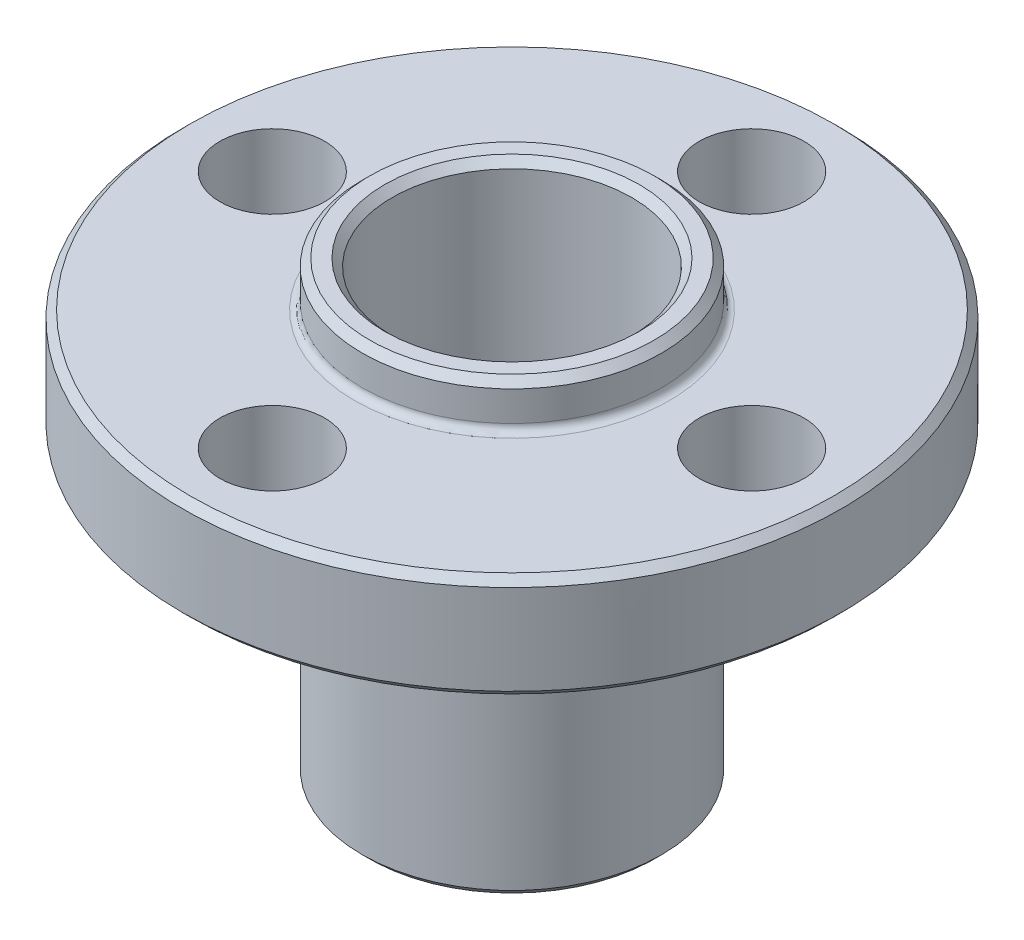
SolidWorks part; units mm, degrees
material "Ottone"
ref_plane "Piano frontale" through (0, 0, 0) normal (0, 0, 1) x (1, 0, 0)
ref_plane "Piano superiore" through (0, 0, 0) normal (0, 1, 0) x (1, 0, 0)
ref_plane "Piano destro" through (0, 0, 0) normal (1, 0, 0) x (0, 0, -1)
sketch "Schizzo1" plane through (0, 0, 0) normal (0, 0, 1) x (1, 0, 0)
  line L0 (0, 0) -> (0, 15)
  line L1 (0, 15) -> (1, 15)
  line L2 (1, 15) -> (1, 13.5)
  line L3 (1, 13.5) -> (7, 13.5)
  line L4 (7, 13.5) -> (7, 10)
  line L5 (7, 10) -> (1, 10)
  line L6 (1, 10) -> (1, 0)
  line L7 (0, 0) -> (1, 0)
  line L8 (0, 0) -> (-4, 0) construction
  line L9 (-4, 0) -> (-4, 18.9483) construction
  dimension "D1" = 3.5
  dimension "D2" = 10
  dimension "D3" = 1.5
  dimension "D4" = 1
  dimension "D5" = 7
  dimension "D7" = 4
revolve "Rivoluzione1" add sketch "Schizzo1" angle 360 about L9
sketch "Schizzo2" plane through (0, 13.5, 0) normal (0, 1, 0) x (1, 0, 0)
  line L0 (-4, 0) -> (-4, -29.8161) construction
  circle A0 centre (-4, -8) radius 1.75
  circle A1 centre (-12, 0) radius 1.75
  circle A2 centre (-4, 8) radius 1.75
  circle A3 centre (4, 0) radius 1.75
  point P6 (-4, 0)
  point P13 (-4, 0)
  dimension "D2" = 3.5
  dimension "D1" = 8
  dimension "D3" = 4
extrude "Taglio-Estrusione1" cut sketch "Schizzo2" against normal blind 10
chamfer "Smusso1" distance 0.25 angle 45 5 edges at (-4, 15, -4) (-4, 15, -5) (-4, 0, -5) (-4, 10, -11) (-4, 13.5, -11)
fillet "Raccordo1" radius 0.25 2 edges at (-4, 13.5, -5) (-4, 10, -5)
